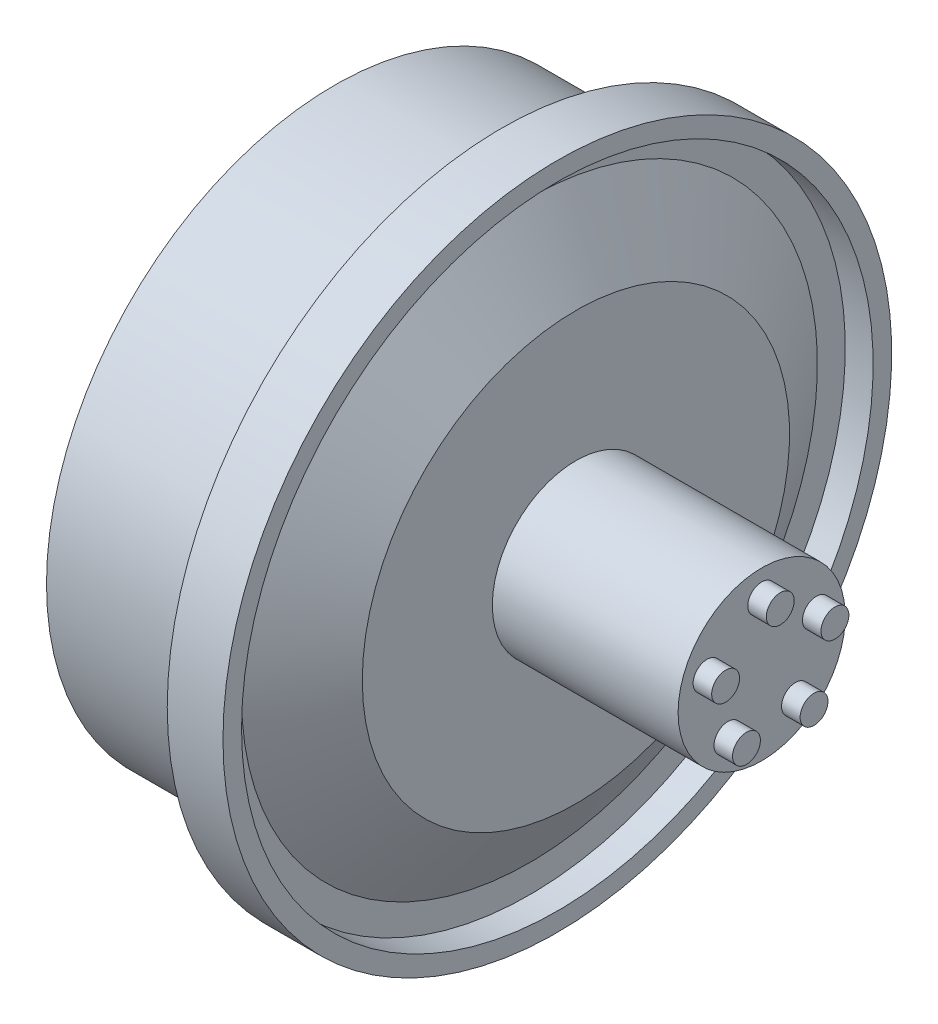
SolidWorks part; units mm, degrees
ref_plane "Front Plane" through (0, 0, 0) normal (0, 0, 1) x (1, 0, 0)
ref_plane "Top Plane" through (0, 0, 0) normal (0, 1, 0) x (1, 0, 0)
ref_plane "Right Plane" through (0, 0, 0) normal (1, 0, 0) x (0, 0, -1)
sketch "Sketch1" plane through (0, 0, 0) normal (0, 1, 0) x (1, 0, 0)
  line L0 (-25, 0) -> (25, 0) construction
  line L1 (-7.6204, 0) -> (-7.6204, 15.5)
  line L2 (-7.6204, 15.5) -> (1.3796, 15.5)
  line L3 (1.3796, 15.5) -> (1.3796, 18)
  line L4 (1.3796, 18) -> (3.3796, 18)
  line L6 (3.3796, 17) -> (2.8796, 17)
  line L7 (2.8796, 17) -> (2.8796, 15.5)
  line L8 (2.8796, 15.5) -> (5.3796, 11.5)
  line L9 (5.3796, 11.5) -> (5.3796, 4.5)
  line L10 (5.3796, 0) -> (-7.6204, 0)
  line L11 (3.3796, 18) -> (4.3796, 18)
  line L12 (4.3796, 18) -> (4.3796, 17)
  line L13 (4.3796, 17) -> (3.3796, 17)
  line L14 (5.3796, 4.5) -> (15.3796, 4.5)
  line L15 (15.3796, 4.5) -> (15.3796, 3.7)
  line L16 (14.5796, 0) -> (5.3796, 0)
  line L20 (15.3796, 3.7) -> (15.3796, 0)
  line L21 (15.3796, 0) -> (14.5796, 0)
  dimension "D1" = 50
  dimension "D2" = 25
  dimension "D3" = 2
  dimension "D4" = 11
  dimension "D5" = 2.5
  dimension "D6" = 36
  dimension "D8" = 1
  dimension "D9" = 1.5
  dimension "D10" = 2.5
  dimension "D11" = 1.5
  dimension "D12" = 1
  dimension "D13" = 9
  dimension "D14" = 10
  dimension "D15" = 0.8
  dimension "D16" = 11.5
revolve "Revolve1" add sketch "Sketch1" angle 360 about L0
sketch "Sketch4" plane through (15.3796, 0, 0) normal (1, 0, 0) x (0, 0, -1)
  circle A0 centre (0, 0) radius 3.0938 construction
  circle A1 centre (0, 3.0938) radius 0.75
  circle A2 centre (2.9424, 0.956) radius 0.75
  circle A3 centre (1.8185, -2.5029) radius 0.75
  circle A4 centre (-1.8185, -2.5029) radius 0.75
  circle A5 centre (-2.9424, 0.956) radius 0.75
  point P16 (0, 0)
  dimension "D1" = 1.5
  dimension "D2" = 5
extrude "Boss-Extrude2" add sketch "Sketch4" along normal blind 1
